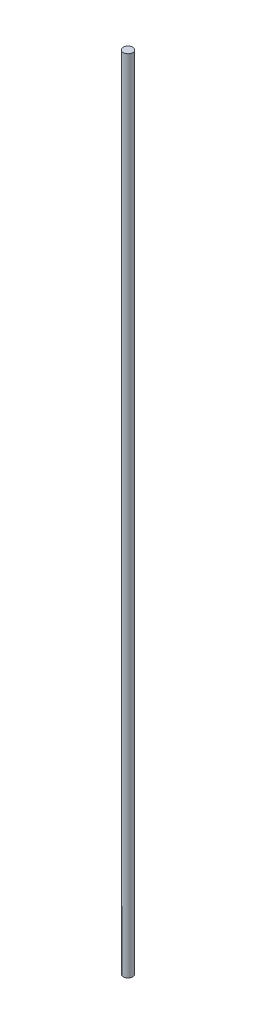
SolidWorks part; units mm, degrees
ref_plane "Front Plane" through (0, 0, 0) normal (0, 0, 1) x (1, 0, 0)
ref_plane "Top Plane" through (0, 0, 0) normal (0, 1, 0) x (1, 0, 0)
ref_plane "Right Plane" through (0, 0, 0) normal (1, 0, 0) x (0, 0, -1)
sketch "Sketch1" plane through (0, 0, 0) normal (0, 1, 0) x (1, 0, 0)
  circle A0 centre (0, 0) radius 2.5
extrude "Boss-Extrude1" add sketch "Sketch1" along normal blind 420
